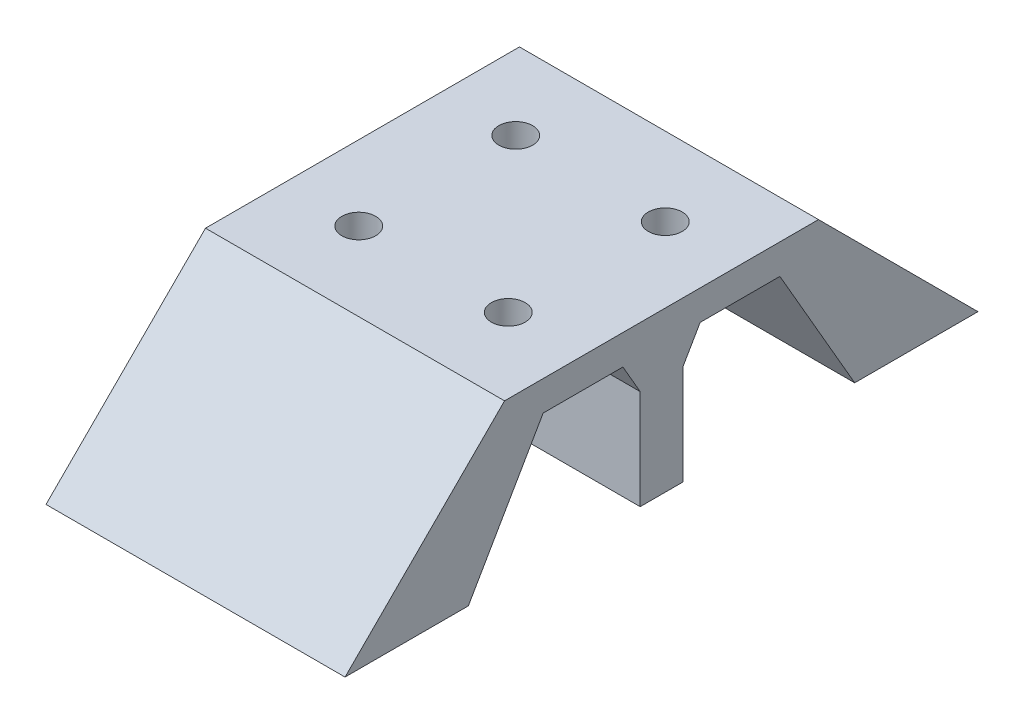
SolidWorks part; units mm, degrees
material "ABS"
ref_plane "Front Plane" through (0, 0, 0) normal (0, 0, 1) x (1, 0, 0)
ref_plane "Top Plane" through (0, 0, 0) normal (0, 1, 0) x (1, 0, 0)
ref_plane "Right Plane" through (0, 0, 0) normal (1, 0, 0) x (0, 0, -1)
sketch "Profile" plane through (0, 0, 0) normal (1, 0, 0) x (0, 0, -1)
  line L0 (-20, 4.405) -> (-20, 9.805) construction
  line L1 (-20, 4.405) -> (20, 4.405) construction
  line L2 (-20, 4.405) -> (-20, 24.405) construction
  line L3 (-20, 24.405) -> (20, 24.405) construction
  line L4 (20, 4.405) -> (20, 24.405) construction
  line L5 (-20, 4.405) -> (20, 24.405) construction
  line L6 (-20, 24.405) -> (20, 4.405) construction
  line L7 (-20, 9.805) -> (-18.5, 11.305) construction
  line L8 (-14.5, 10.6126) -> (-14.5, 18.1974) construction
  line L9 (0, 14.405) -> (-20, 14.405) construction
  line L10 (0, 14.405) -> (0, 4.405) construction
  line L11 (-20, 4.405) -> (-14.6, 4.405) construction
  line L12 (-14.6, 4.405) -> (-13.1, 5.905) construction
  line L13 (-13.1, 5.905) -> (-15.5, 5.905) construction
  line L14 (-15.5, 5.905) -> (-15.5, 7.405) construction
  line L15 (-15.5, 7.405) -> (-13.1, 9.905) construction
  line L16 (-13.1, 9.905) -> (-6.9, 9.905) construction
  line L17 (-6.9, 9.905) -> (-4.5, 7.405) construction
  line L18 (-4.5, 7.405) -> (-4.5, 5.905) construction
  line L19 (-4.5, 5.905) -> (-6.9, 5.905) construction
  line L20 (-6.9, 5.905) -> (-5.4, 4.405) construction
  line L21 (-5.4, 4.405) -> (5.4, 4.405) construction
  line L22 (-3, 5.905) -> (-3, 8.0085) construction
  line L23 (-3, 5.905) -> (3, 5.905) construction
  line L24 (0, 5.905) -> (0, 4.405)
  line L25 (-14.5, 14.405) -> (-12.1, 14.405) construction
  line L26 (-7.9, 14.405) -> (-5.5, 14.405) construction
  line L27 (-5.5, 18.1974) -> (-5.5, 10.6126) construction
  line L28 (-5.5, 10.6126) -> (-3, 8.0085) construction
  line L29 (-13.1, 9.905) -> (-13.1, 5.905) construction
  line L30 (-13.1, 5.905) -> (-6.9, 5.905) construction
  line L31 (-6.9, 9.905) -> (-6.9, 5.905) construction
  line L32 (-18.5, 11.305) -> (-18.5, 8.0085) construction
  line L33 (-18.5, 8.0085) -> (-17, 8.0085) construction
  line L34 (-15.5, 7.405) -> (-4.5, 7.405) construction
  line L35 (-17, 8.0085) -> (-14.5, 10.6126) construction
  line L36 (-13.1, 9.905) -> (-6.9, 9.905) construction
  line L37 (-10, 9.905) -> (-10, 14.405) construction
  line L38 (-18.5, 8.0085) -> (-20, 8.0085) construction
  line L39 (-15.5, 5.905) -> (-15.5, 4.405) construction
  line L40 (-4.5, 5.905) -> (-4.5, 4.405) construction
  line L41 (-17, 8.0085) -> (-3, 8.0085) construction
  line L42 (-18.5, 11.305) -> (-20, 11.305) construction
  line L43 (-18.5, 20.8015) -> (-17, 20.8015) construction
  line L44 (-18.5, 17.505) -> (-18.5, 20.8015) construction
  line L45 (-20, 19.005) -> (-18.5, 17.505) construction
  line L46 (-20, 24.405) -> (-20, 19.005) construction
  line L47 (-20, 24.405) -> (-14.6, 24.405) construction
  line L48 (-14.6, 24.405) -> (-13.1, 22.905) construction
  line L49 (-13.1, 22.905) -> (-15.5, 22.905) construction
  line L50 (-15.5, 22.905) -> (-15.5, 21.405) construction
  line L51 (-15.5, 21.405) -> (-13.1, 18.905) construction
  line L52 (-13.1, 18.905) -> (-6.9, 18.905) construction
  line L53 (-6.9, 18.905) -> (-4.5, 21.405) construction
  line L54 (-4.5, 21.405) -> (-4.5, 22.905) construction
  line L55 (-4.5, 22.905) -> (-6.9, 22.905) construction
  line L56 (-6.9, 22.905) -> (-5.4, 24.405) construction
  line L57 (-5.4, 24.405) -> (5.4, 24.405) construction
  line L58 (0, 22.905) -> (0, 24.405)
  line L59 (-3, 22.905) -> (3, 22.905) construction
  line L60 (-3, 22.905) -> (-3, 20.8015) construction
  line L61 (-5.5, 18.1974) -> (-3, 20.8015) construction
  line L62 (-17, 20.8015) -> (-14.5, 18.1974) construction
  line L63 (18.5, 17.505) -> (18.5, 20.8015) construction
  line L64 (20, 19.005) -> (18.5, 17.505) construction
  line L65 (20, 24.405) -> (20, 19.005) construction
  line L66 (20, 24.405) -> (14.6, 24.405) construction
  line L67 (14.6, 24.405) -> (13.1, 22.905) construction
  line L68 (13.1, 22.905) -> (15.5, 22.905) construction
  line L69 (15.5, 22.905) -> (15.5, 21.405) construction
  line L70 (15.5, 21.405) -> (13.1, 18.905) construction
  line L71 (13.1, 18.905) -> (6.9, 18.905) construction
  line L72 (6.9, 18.905) -> (4.5, 21.405) construction
  line L73 (4.5, 21.405) -> (4.5, 22.905) construction
  line L74 (4.5, 22.905) -> (6.9, 22.905) construction
  line L75 (6.9, 22.905) -> (5.4, 24.405) construction
  line L76 (3, 22.905) -> (3, 20.8015) construction
  line L77 (5.5, 18.1974) -> (3, 20.8015) construction
  line L78 (5.5, 18.1974) -> (5.5, 10.6126) construction
  line L79 (5.5, 10.6126) -> (3, 8.0085) construction
  line L80 (3, 5.905) -> (3, 8.0085) construction
  line L81 (6.9, 5.905) -> (5.4, 4.405) construction
  line L82 (4.5, 5.905) -> (6.9, 5.905) construction
  line L83 (4.5, 7.405) -> (4.5, 5.905) construction
  line L84 (6.9, 9.905) -> (4.5, 7.405) construction
  line L85 (13.1, 9.905) -> (6.9, 9.905) construction
  line L86 (15.5, 7.405) -> (13.1, 9.905) construction
  line L87 (15.5, 5.905) -> (15.5, 7.405) construction
  line L88 (13.1, 5.905) -> (15.5, 5.905) construction
  line L89 (14.6, 4.405) -> (13.1, 5.905) construction
  line L90 (20, 4.405) -> (14.6, 4.405) construction
  line L91 (20, 4.405) -> (20, 9.805) construction
  line L92 (20, 9.805) -> (18.5, 11.305) construction
  line L93 (18.5, 11.305) -> (18.5, 8.0085) construction
  line L94 (18.5, 8.0085) -> (17, 8.0085) construction
  line L95 (17, 8.0085) -> (14.5, 10.6126) construction
  line L96 (14.5, 10.6126) -> (14.5, 18.1974) construction
  line L97 (17, 20.8015) -> (14.5, 18.1974) construction
  line L98 (18.5, 20.8015) -> (17, 20.8015) construction
  line L99 (-20, 1.905) -> (-23.81, -1.905)
  line L100 (20, 1.905) -> (-20, 1.905)
  line L101 (20, 1.905) -> (20, -1.905) construction
  line L103 (-20, 1.905) -> (-20, -1.905) construction
  line L104 (20, 1.905) -> (-20, -1.905) construction
  line L105 (20, -1.905) -> (-20, 1.905) construction
  line L106 (-23.81, -1.905) -> (-20, -1.905) construction
  line L107 (20, -1.905) -> (23.81, -1.905) construction
  line L108 (23.81, -1.905) -> (20, 1.905)
  line L115 (14.6, 4.405) -> (14.6, -1.905) construction
  line L116 (5.4, 4.405) -> (5.4, -1.905) construction
  line L117 (-14.6, 4.405) -> (-14.6, -1.905) construction
  line L118 (-5.4, 4.405) -> (-5.4, -1.905) construction
  line L119 (-20, -1.905) -> (-14.6, -1.905) construction
  line L120 (-5.4, -1.905) -> (5.4, -1.905) construction
  line L121 (14.6, -1.905) -> (20, -1.905) construction
  line L122 (14.6, -1.905) -> (5.4, -1.905)
  line L123 (-5.4, -1.905) -> (-14.6, -1.905)
  line L124 (23.81, -1.905) -> (27.62, -5.715)
  line L129 (4.92, -1.905) -> (2.7203, -5.715)
  line L130 (2.7203, -5.715) -> (-2.7203, -5.715) construction
  line L131 (27.62, -5.715) -> (20, -5.715) construction
  line L132 (20, -5.715) -> (20, -1.905) construction
  line L133 (-20, -1.905) -> (-20, -5.715) construction
  line L134 (-20, -5.715) -> (-27.62, -5.715) construction
  line L135 (-27.62, -5.715) -> (-23.81, -1.905)
  line L136 (-2.7203, -5.715) -> (-4.92, -1.905)
  line L137 (20, -5.715) -> (17.2797, -5.715) construction
  line L138 (17.2797, -5.715) -> (15.08, -1.905)
  line L139 (0, 0) -> (0, -5.715) construction
  line L140 (-20, -5.715) -> (-17.2797, -5.715) construction
  line L141 (-17.2797, -5.715) -> (-15.08, -1.905)
  line L142 (15.08, -1.905) -> (14.6, -1.905)
  line L143 (-15.08, -1.905) -> (-14.6, -1.905)
  line L144 (5.4, -1.905) -> (4.92, -1.905)
  line L145 (-4.92, -1.905) -> (-5.4, -1.905)
  line L146 (27.62, -5.715) -> (35.24, -13.335)
  line L147 (17.2797, -5.715) -> (21.6791, -13.335)
  line L148 (21.6791, -13.335) -> (35.24, -13.335) construction
  line L149 (2.7203, -5.715) -> (2.7203, -13.335)
  line L150 (2.7203, -13.335) -> (-2.7203, -13.335) construction
  line L151 (-2.7203, -13.335) -> (-2.7203, -5.715)
  line L152 (-17.2797, -5.715) -> (-21.6791, -13.335)
  line L153 (-27.62, -5.715) -> (-35.24, -13.335)
  line L154 (-35.24, -13.335) -> (-21.6791, -13.335) construction
  line L155 (35.24, -13.335) -> (40.32, -18.415)
  line L156 (21.6791, -13.335) -> (24.6121, -18.415)
  line L157 (40.32, -18.415) -> (24.6121, -18.415)
  line L158 (2.7203, -13.335) -> (2.7203, -18.415)
  line L159 (2.7203, -18.415) -> (-2.7203, -18.415)
  line L160 (-2.7203, -18.415) -> (-2.7203, -13.335)
  line L161 (-21.6791, -13.335) -> (-24.6121, -18.415)
  line L162 (-35.24, -13.335) -> (-40.32, -18.415)
  line L163 (-40.32, -18.415) -> (-24.6121, -18.415)
  circle A0 centre (-10, 14.405) radius 2.1 construction
  circle A1 centre (10, 14.405) radius 2.1 construction
  point P0 (0, 14.405)
  point P97 (-10, -1.905)
  point P105 (0, 0)
  point P106 (10, -1.905)
  dimension "D3" = 2.1
  dimension "D1" = 40
  dimension "D2" = 20
  dimension "D4" = 45
  dimension "D5" = 45
  dimension "D6" = 1.5
  dimension "D7" = 6.2
  dimension "D8" = 11
  dimension "D9" = 45
  dimension "D10" = 10
  dimension "D11" = 1.5
  dimension "D12" = 3.1
  dimension "D13" = 5.5
  dimension "D14" = 5.5
  dimension "D15" = 1.5
  dimension "D16" = 1.5
  dimension "D17" = 3.81
  dimension "D18" = 45
  dimension "D19" = 45
  dimension "D20" = 2.5
  dimension "D21" = 3.81
  dimension "D22" = 5.08
  dimension "D23" = 5.08
  dimension "D24" = 60
  dimension "D25" = 60
  dimension "D26" = 7.62
  dimension "D27" = 5.08
extrude "Body" add sketch "Profile" along normal blind 38.1
sketch "Hole Layout" plane through (0, -1.905, 0) normal (0, -1, 0) x (1, 0, 0)
  line L0 (0, -10) -> (38.1, -10) construction
  line L2 (38.1, -15.08) -> (38.1, -4.92) construction
  line L3 (19.05, -10) -> (19.05, 10) construction
  line L4 (0, 10) -> (19.05, 10) construction
  line L9 (0, 4.92) -> (0, 15.08) construction
  line L12 (28.575, -10) -> (9.525, -10) construction
  line L13 (28.575, -10) -> (28.575, 10) construction
  line L14 (28.575, 10) -> (9.525, 10) construction
  line L15 (9.525, -10) -> (9.525, 10) construction
  line L16 (28.575, -10) -> (9.525, 10) construction
  line L17 (28.575, 10) -> (9.525, -10) construction
  point P10 (19.05, 0)
hole_wizard "13/64 (0.20313) Diameter Hole1" positions "Sketch4" profile "Sketch5" hole size "13/64" standard "ANSI Inch"
sketch "Sketch4" plane through (0, -1.905, 0) normal (0, -1, 0) x (-1, 0, 0)
  point P32 (-9.525, 10)
  point P35 (-9.525, -10)
  point P38 (-28.575, -10)
  point P41 (-28.575, 10)
sketch "Sketch5" plane through (9.525, -1.905, -10) normal (1, 0, 0) x (0, 0, -1)
  line L0 (0, 0) -> (0, 5.1061)
  line L1 (0, 5.1061) -> (2.5798, 3.556)
  line L2 (2.5798, 3.556) -> (2.5798, 0)
  line L5 (2.5798, 0) -> (0, 0)
  line L10 (0, 5.1061) -> (-2.5798, 3.556) construction
  line L11 (0, -6.35) -> (0, 107.95) construction
  dimension "Hole Dia." = 5.1595
  dimension "Hole Depth" = 3.556
  dimension "Drill Angle" = 118
chamfer "Chamfer1" distance 0.635 angle 30 4 edges at (9.525, -1.905, 7.4202) (28.575, -1.905, 7.4202) (28.575, -1.905, -12.5798) (9.525, -1.905, -12.5798)
